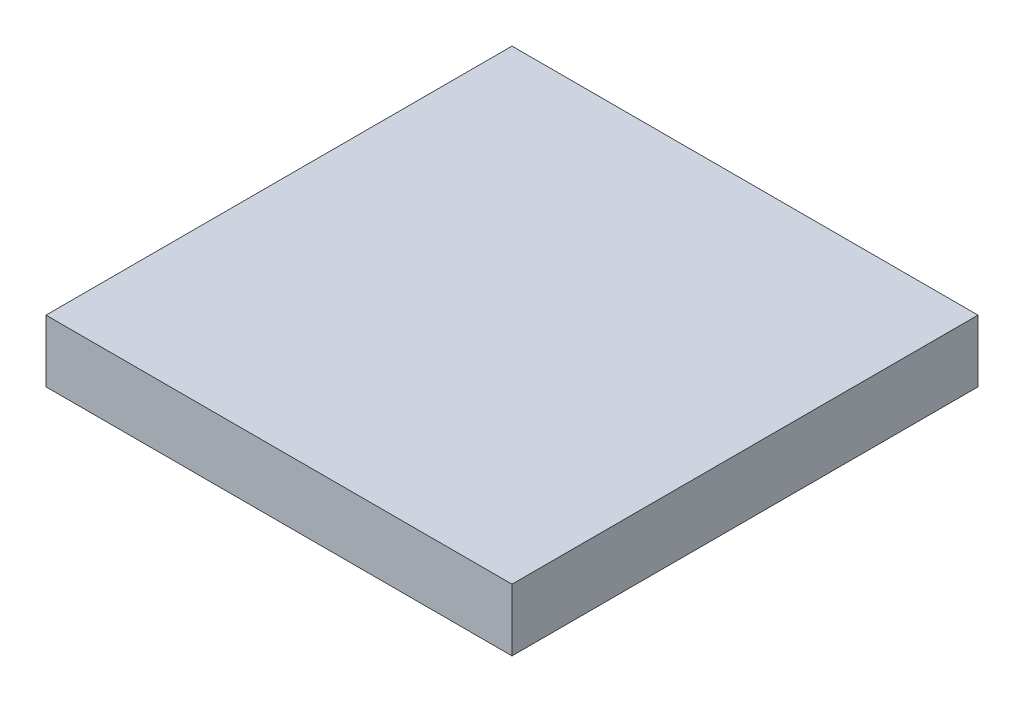
SolidWorks part; units mm, degrees
ref_plane "Front Plane" through (0, 0, 0) normal (0, 0, 1) x (1, 0, 0)
ref_plane "Top Plane" through (0, 0, 0) normal (0, 1, 0) x (1, 0, 0)
ref_plane "Right Plane" through (0, 0, 0) normal (1, 0, 0) x (0, 0, -1)
sketch "Sketch1" plane through (0, 0, 0) normal (0, 1, 0) x (1, 0, 0)
  line L1 (-128.9655, 82.7586) -> (171.0345, 82.7586)
  line L2 (-128.9655, 82.7586) -> (-128.9655, -217.2414)
  line L3 (-128.9655, -217.2414) -> (171.0345, -217.2414)
  line L4 (171.0345, 82.7586) -> (171.0345, -217.2414)
  dimension "D1" = 300
  dimension "D2" = 300
extrude "Boss-Extrude1" add sketch "Sketch1" along normal blind 40
